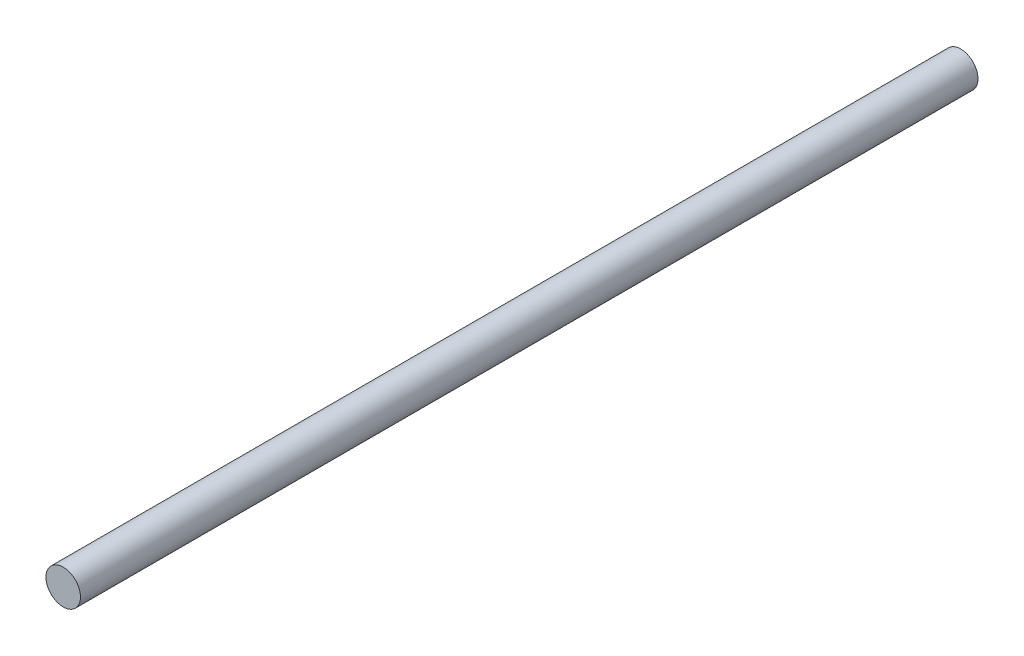
SolidWorks part; units mm, degrees
ref_plane "Płaszczyzna przednia" through (0, 0, 0) normal (0, 0, 1) x (1, 0, 0)
ref_plane "Płaszczyzna górna" through (0, 0, 0) normal (0, 1, 0) x (1, 0, 0)
ref_plane "Płaszczyzna prawa" through (0, 0, 0) normal (1, 0, 0) x (0, 0, -1)
sketch "Sketch1" plane through (0, 0, 0) normal (0, 0, 1) x (1, 0, 0)
  circle A4 centre (0, 0) radius 10
  dimension "D1" = 20
extrude "Boss-Extrude1" add sketch "Sketch1" along normal blind 520
